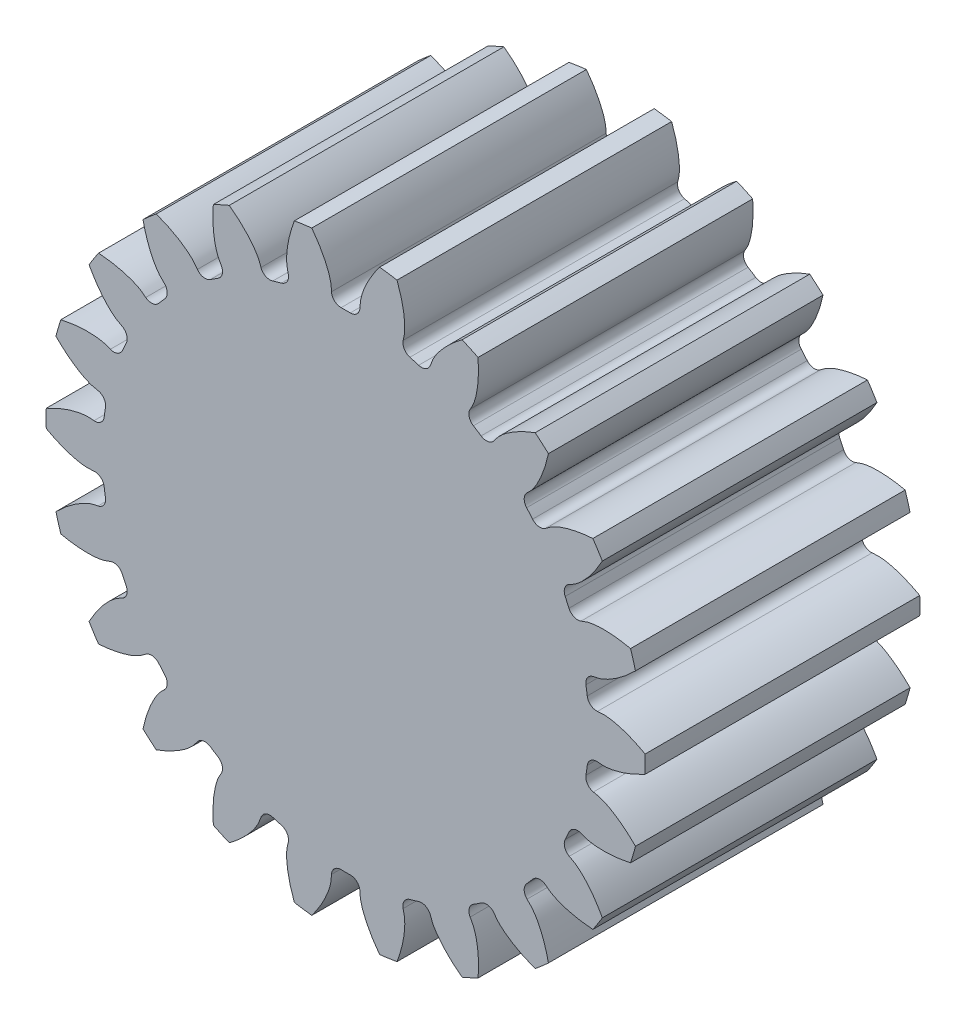
SolidWorks part; units mm, degrees
ref_plane "前视基准面" through (0, 0, 0) normal (0, 0, 1) x (1, 0, 0)
ref_plane "上视基准面" through (0, 0, 0) normal (0, 1, 0) x (1, 0, 0)
ref_plane "右视基准面" through (0, 0, 0) normal (1, 0, 0) x (0, 0, -1)
ref_axis "Axis1" through (0, 0, -88.99) along (0, 0, 1)
sketch "草图1" plane through (0, 0, 0) normal (0, 0, 1) x (1, 0, 0)
  circle A0 centre (0, 0) radius 12
extrude "LaShenA" add sketch "草图1" along normal blind 11
sketch "SketchA" plane through (0, 0, 11) normal (0, 0, 1) x (1, 0, 0)
  line L0 (0, 0) -> (0, 12) construction
  arc A0 (0.1829, 9.7483) -> (-0.1829, 9.7483) centre (0, 0) ccw
  arc A1 (1.7922, 12.4394) -> (-1.7922, 12.4394) centre (0, 0) ccw
  arc A2 (-0.1829, 9.7483) -> (-0.5693, 10.1058) centre (-0.19, 10.1282) cw
  arc A3 (0.5693, 10.1058) -> (0.1829, 9.7483) centre (0.19, 10.1282) cw
  circle A4 centre (0, 0) radius 10.3366 construction
  circle A5 centre (0, 0) radius 12 construction
  circle A6 centre (0, 0) radius 9.75 construction
  circle A7 centre (0, 0) radius 11 construction
  spline S0 degree 3 poles (0.5693, 10.1058) (0.5736, 10.1777) (0.5776, 10.2793) (0.5937, 10.3939) (0.606, 10.4523) (0.6168, 10.4986) (0.6308, 10.5517) (0.6482, 10.6114) (0.6693, 10.6775) (0.6947, 10.75) (0.7246, 10.8287) (0.7593, 10.9132) (0.7992, 11.0036) (0.8447, 11.0994) (0.8959, 11.2005) (0.9533, 11.3067) (1.0172, 11.4176) (1.0878, 11.533) (1.1655, 11.6527) (1.2504, 11.7762) (1.3429, 11.9034) (1.4432, 12.0339) (1.5907, 12.2156) (1.7093, 12.3501) (1.7922, 12.4394) knots 0.122554 0.122554 0.122554 0.122554 0.192705 0.222547 0.235684 0.251209 0.269123 0.289425 0.312116 0.337195 0.364662 0.394518 0.426763 0.461396 0.498418 0.537828 0.579626 0.623813 0.670389 0.719353 0.770705 0.824446 0.880576 1 1 1 1
  spline S1 degree 3 poles (-0.5693, 10.1058) (-0.5736, 10.1777) (-0.5776, 10.2793) (-0.5937, 10.3939) (-0.606, 10.4523) (-0.6168, 10.4986) (-0.6308, 10.5517) (-0.6482, 10.6114) (-0.6693, 10.6775) (-0.6947, 10.75) (-0.7246, 10.8287) (-0.7593, 10.9132) (-0.7992, 11.0036) (-0.8447, 11.0994) (-0.8959, 11.2005) (-0.9533, 11.3067) (-1.0172, 11.4176) (-1.0878, 11.533) (-1.1655, 11.6527) (-1.2504, 11.7762) (-1.3429, 11.9034) (-1.4432, 12.0339) (-1.5907, 12.2156) (-1.7093, 12.3501) (-1.7922, 12.4394) knots 0.122554 0.122554 0.122554 0.122554 0.192705 0.222547 0.235684 0.251209 0.269123 0.289425 0.312116 0.337195 0.364662 0.394518 0.426763 0.461396 0.498418 0.537828 0.579626 0.623813 0.670389 0.719353 0.770705 0.824446 0.880576 1 1 1 1
  dimension "D1" = 0.38
  dimension "Db" = 20.6732
  dimension "Da" = 24
  dimension "Df" = 19.5
  dimension "Dn" = 22
extrude "Cut-ExtrudeA" cut sketch "SketchA" against normal blind 11
pattern_circular "www.KYTool.cn" count 22 over 360 about axis through (0, 0, -88.99) along (0, 0, 1) of "Cut-ExtrudeA"
